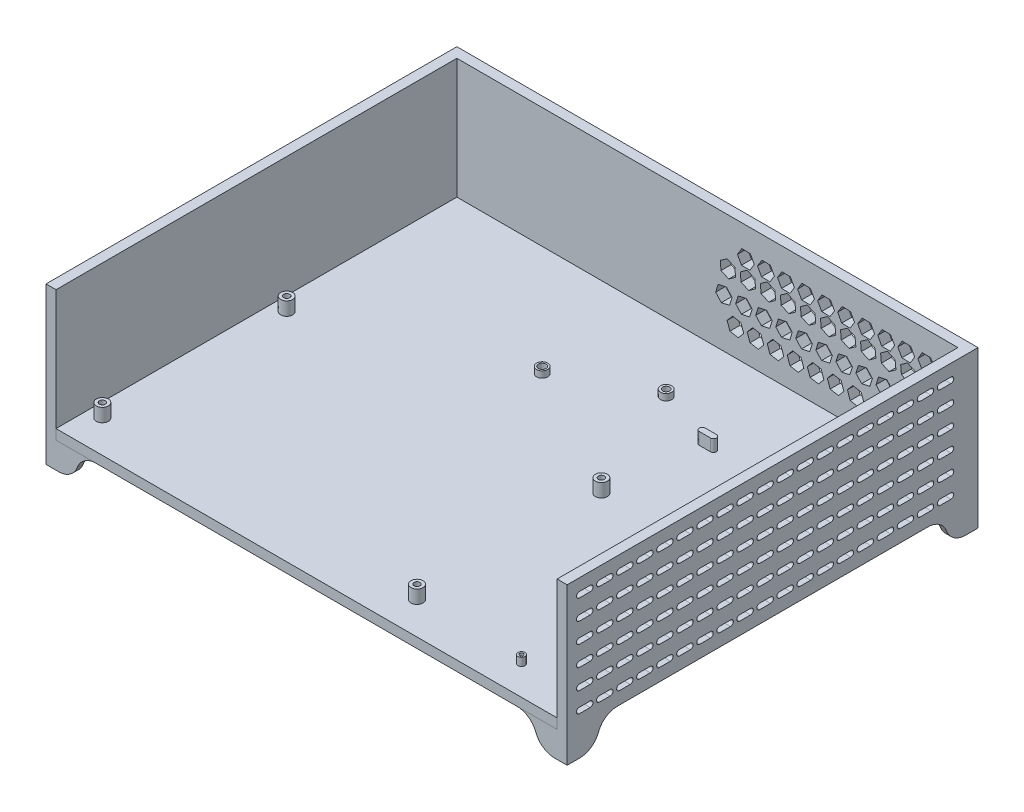
SolidWorks part; units mm, degrees
material "Balsa"
ref_plane "Front Plane" through (0, 0, 0) normal (0, 0, 1) x (1, 0, 0)
ref_plane "Top Plane" through (0, 0, 0) normal (0, 1, 0) x (1, 0, 0)
ref_plane "Right Plane" through (0, 0, 0) normal (1, 0, 0) x (0, 0, -1)
sketch "Sketch2" plane through (0, 0, 0) normal (0, 1, 0) x (1, 0, 0)
  line L1 (-117.3267, 56.1881) -> (132.6733, 56.1881)
  line L2 (-117.3267, 56.1881) -> (-117.3267, -143.8119)
  line L3 (-117.3267, -143.8119) -> (132.6733, -143.8119)
  line L4 (132.6733, 56.1881) -> (132.6733, -143.8119)
  dimension "D1" = 250
  dimension "D2" = 200
extrude "Boss-Extrude1" add sketch "Sketch2" along normal blind 5
sketch "Sketch3" plane through (0, 5, 0) normal (0, 1, 0) x (1, 0, 0)
  line L0 (132.6733, 56.1881) -> (-117.3267, 56.1881) construction
  line L1 (137.6733, -143.7988) -> (-122.3267, -143.7988)
  line L2 (137.6733, -143.7988) -> (137.6733, 61.1881)
  line L3 (137.6733, 61.1881) -> (-122.3267, 61.1881)
  line L4 (-122.3267, -143.7988) -> (-122.3267, 61.1881)
  line L5 (-117.3267, 56.1881) -> (-117.3267, -143.8119) construction
  line L6 (132.6733, -143.8119) -> (132.6733, 56.1881) construction
  line L7 (137.6733, -143.7988) -> (-117.3267, -143.7988)
  line L8 (137.6733, -143.7988) -> (137.6733, 56.1881)
  line L9 (137.6733, 56.1881) -> (-117.3267, 56.1881)
  line L10 (-117.3267, -143.7988) -> (-117.3267, 56.1881)
  point P7 (-122.3267, -41.3053)
  line M5 (-117.3267, 56.1881) -> (-117.3267, -143.8119)
  line M7 (132.6733, -143.8119) -> (132.6733, 56.1881)
  line M8 (132.6733, 56.1881) -> (-117.3267, 56.1881)
  dimension "D1" = 5
  dimension "D2" = 5
  dimension "D3" = 5
extrude "Boss-Extrude2" add sketch "Sketch3" along normal blind 60 and the other way blind 5 contours L9 L2 L3 L4 L1 M5 M8 | L2 L9 L1 M7
sketch "Sketch4" plane through (0, 5, 0) normal (0, 1, 0) x (1, 0, 0)
  line L0 (120.5422, 10.8082) -> (125.8032, 10.8082) construction
  line L1 (120.5422, 12.4303) -> (125.8032, 12.4303)
  line L2 (120.5422, 9.186) -> (125.8032, 9.186)
  line L3 (50.3793, 10.8952) -> (56.0063, 10.8952) construction
  line L4 (50.3793, 12.3842) -> (56.0063, 12.3842)
  line L5 (50.3793, 9.4062) -> (56.0063, 9.4062)
  arc A0 (120.5422, 12.4303) -> (120.5422, 9.186) centre (120.5422, 10.8082) ccw
  arc A1 (125.8032, 9.186) -> (125.8032, 12.4303) centre (125.8032, 10.8082) ccw
  arc A2 (50.3793, 12.3842) -> (50.3793, 9.4062) centre (50.3793, 10.8952) ccw
  arc A3 (56.0063, 9.4062) -> (56.0063, 12.3842) centre (56.0063, 10.8952) ccw
  point P2 (123.1727, 10.8082)
  point P7 (53.1928, 10.8952)
extrude "Boss-Extrude3" add sketch "Sketch4" along normal blind 6
sketch "Sketch5" plane through (0, 5, 0) normal (0, 1, 0) x (1, 0, 0)
  circle A0 centre (-110.3764, -127.6498) radius 1.5
  circle A1 centre (-110.3764, -127.6498) radius 3
  circle A2 centre (-110.3764, -35.6498) radius 1.5
  circle A3 centre (-110.3764, -35.6498) radius 3
  circle A4 centre (46.6236, -35.6498) radius 1.5
  circle A5 centre (46.6236, -35.6498) radius 3
  circle A6 centre (46.6236, -127.6498) radius 1.5
  circle A7 centre (46.6236, -127.6498) radius 3
extrude "Boss-Extrude4" add sketch "Sketch5" along normal blind 6.68
sketch "Sketch6" plane through (0, 5, 0) normal (0, 1, 0) x (1, 0, 0)
  circle A0 centre (-19.7726, 1.1756) radius 1.9189
  circle A1 centre (-19.7726, 1.1756) radius 2.7795
  circle A2 centre (20.9839, 22.296) radius 1.7201
  circle A3 centre (20.9839, 22.296) radius 2.8027
extrude "Boss-Extrude5" add sketch "Sketch6" along normal blind 3.2
sketch "Sketch7" plane through (0, 5, 0) normal (0, 1, 0) x (1, 0, 0)
  circle A0 centre (124.7627, -88.1501) radius 1.1545
  circle A1 centre (124.7627, -88.1501) radius 1.8195
  circle A2 centre (100.3757, -129.281) radius 0.9299
  circle A3 centre (100.3757, -129.281) radius 1.7427
extrude "Boss-Extrude6" add sketch "Sketch7" along normal blind 4
sketch "Sketch8" plane through (137.6733, 0, 0) normal (1, 0, 0) x (0, 0, -1)
  line L0 (-137.7294, 57.6356) -> (-132.3053, 57.6356) construction
  line L1 (-137.7294, 59.036) -> (-132.3053, 59.036)
  line L2 (-137.7294, 56.2352) -> (-132.3053, 56.2352)
  arc A0 (-137.7294, 59.036) -> (-137.7294, 56.2352) centre (-137.7294, 57.6356) ccw
  arc A1 (-132.3053, 56.2352) -> (-132.3053, 59.036) centre (-132.3053, 57.6356) ccw
  point P2 (-135.0173, 57.6356)
extrude "Cut-Extrude1" cut sketch "Sketch8" against normal blind 10
pattern_linear "LPattern1" count 19 spacing 10 along (0, 0, -1) of "Cut-Extrude1"
pattern_linear "LPattern2" count 6 spacing 10 along (0, -1, 0) of "LPattern1", "Cut-Extrude1"
sketch "Sketch9" plane through (0, 0, -61.1881) normal (0, 0, -1) x (-1, 0, 0)
  line L1 (-124.8582, 53.8838) -> (-129.0669, 53.7733)
  line L2 (-129.0669, 53.7733) -> (-131.0756, 50.0732)
  line L3 (-131.0756, 50.0732) -> (-128.8755, 46.4836)
  line L4 (-128.8755, 46.4836) -> (-124.6668, 46.5941)
  line L5 (-124.6668, 46.5941) -> (-122.6581, 50.2942)
  line L6 (-122.6581, 50.2942) -> (-124.8582, 53.8838)
  circle A0 centre (-126.8668, 50.1837) radius 3.6461 construction
extrude "Cut-Extrude2" cut sketch "Sketch9" against normal blind 10
pattern_circular "CirPattern1" count 4 every 37 about axis through (135.1733, 32.5, 0) along (0, 0, 1) of "Cut-Extrude2"
pattern_linear "LPattern3" count 11 spacing 10 along (-1, 0, 0) of "CirPattern1", "Cut-Extrude2"
sketch "Sketch10" plane through (0, 0, 0) normal (0, -1, 0) x (-1, 0, 0)
  line L1 (122.3267, -143.7988) -> (107.3267, -143.7988)
  line L2 (122.3267, -143.7988) -> (122.3267, -140.7988)
  line L3 (122.3267, -140.7988) -> (107.3267, -140.7988)
  line L4 (107.3267, -143.7988) -> (107.3267, -140.7988)
  line L5 (122.3267, -143.7988) -> (119.3267, -143.7988)
  line L6 (122.3267, -143.7988) -> (122.3267, -128.7988)
  line L7 (122.3267, -128.7988) -> (119.3267, -128.7988)
  line L8 (119.3267, -143.7988) -> (119.3267, -128.7988)
  line L9 (-137.6733, -143.7988) -> (-122.6733, -143.7988)
  line L10 (-137.6733, -143.7988) -> (-137.6733, -140.7988)
  line L11 (-137.6733, -140.7988) -> (-122.6733, -140.7988)
  line L12 (-122.6733, -143.7988) -> (-122.6733, -140.7988)
  line L13 (-137.6733, -143.7988) -> (-134.6733, -143.7988)
  line L14 (-137.6733, -143.7988) -> (-137.6733, -128.7988)
  line L15 (-137.6733, -128.7988) -> (-134.6733, -128.7988)
  line L16 (-134.6733, -143.7988) -> (-134.6733, -128.7988)
  line L17 (122.3267, 61.1881) -> (119.3267, 61.1881)
  line L18 (122.3267, 61.1881) -> (122.3267, 46.1881)
  line L19 (122.3267, 46.1881) -> (119.3267, 46.1881)
  line L20 (119.3267, 61.1881) -> (119.3267, 46.1881)
  line L21 (122.3267, 61.1881) -> (107.3267, 61.1881)
  line L22 (122.3267, 61.1881) -> (122.3267, 58.1881)
  line L23 (122.3267, 58.1881) -> (107.3267, 58.1881)
  line L24 (107.3267, 61.1881) -> (107.3267, 58.1881)
  line L25 (-137.6733, 61.1881) -> (-122.6733, 61.1881)
  line L26 (-137.6733, 61.1881) -> (-137.6733, 58.1881)
  line L27 (-137.6733, 58.1881) -> (-122.6733, 58.1881)
  line L28 (-122.6733, 61.1881) -> (-122.6733, 58.1881)
  line L29 (-137.6733, 61.1881) -> (-134.6733, 61.1881)
  line L30 (-137.6733, 61.1881) -> (-137.6733, 46.1881)
  line L31 (-137.6733, 46.1881) -> (-134.6733, 46.1881)
  line L32 (-134.6733, 61.1881) -> (-134.6733, 46.1881)
  line M18 (117.3267, -143.7988) -> (122.3267, -143.7988)
  line M19 (122.3267, -143.7988) -> (122.3267, 61.1881)
  line M20 (122.3267, 61.1881) -> (-137.6733, 61.1881)
  line M21 (-137.6733, 61.1881) -> (-137.6733, -143.7988)
  line M22 (-137.6733, -143.7988) -> (-132.6733, -143.7988)
  dimension "D1" = 3
  dimension "D2" = 3
  dimension "D3" = 15
  dimension "D4" = 15
  dimension "D5" = 3
  dimension "D6" = 3
  dimension "D7" = 15
  dimension "D8" = 15
  dimension "D9" = 3
  dimension "D10" = 3
  dimension "D11" = 15
  dimension "D12" = 15
  dimension "D13" = 3
  dimension "D14" = 3
  dimension "D15" = 15
  dimension "D16" = 15
extrude "Boss-Extrude7" add sketch "Sketch10" along normal blind 13 contours L8 L3 L4 L1 M18 | L8 L1 L3 M19 | L8 L3 L7 M19 | L23 L20 L19 M19 | L23 L18 L20 M20 | L24 L23 L20 M20 | L32 L27 L28 M20 | L32 L27 L31 M21 | L32 L25 L27 M21 | L16 L9 L12 L11 | L16 L11 M22 M21 | L11 L16 L15 M21
fillet "Fillet1" radius 10 8 edges at (136.1733, 0, 128.7988) (122.6733, 0, 142.2988) (136.1733, 0, -46.1881) (122.6733, 0, -59.6881) (-120.8267, 0, -46.1881) (-107.3267, 0, -59.6881) (-107.3267, 0, 142.2988) (-120.8267, 0, 128.7988)
fillet "Fillet2" radius 10 8 edges at (-107.3267, -13, 142.2988) (-120.8267, -13, 128.7988) (136.1733, -13, 128.7988) (122.6733, -13, 142.2988) (122.6733, -13, -59.6881) (136.1733, -13, -46.1881) (-107.3267, -13, -59.6881) (-120.8267, -13, -46.1881)
